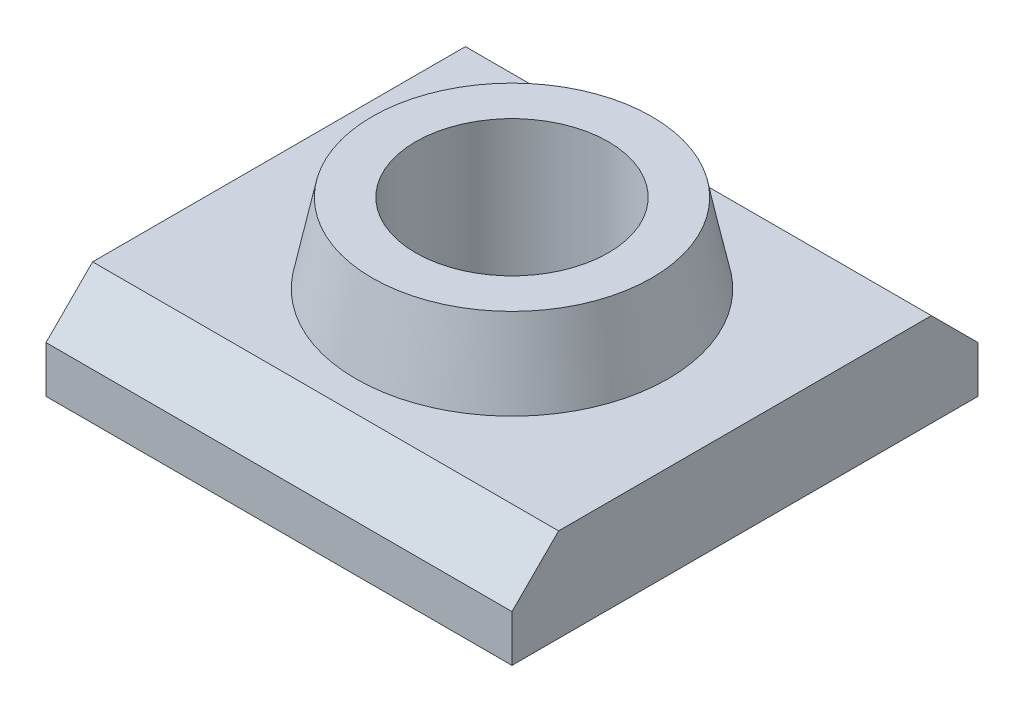
SolidWorks part; units mm, degrees
ref_plane "Front Plane" through (0, 0, 0) normal (0, 0, 1) x (1, 0, 0)
ref_plane "Top Plane" through (0, 0, 0) normal (0, 1, 0) x (1, 0, 0)
ref_plane "Right Plane" through (0, 0, 0) normal (1, 0, 0) x (0, 0, -1)
ref_plane "Plane1" through (-5, 0, 0) normal (1, 0, 0) x (0, 0, -1)
sketch "Sketch1" plane through (-5, 0, 0) normal (1, 0, 0) x (0, 0, -1)
  line L0 (4, -1.7) -> (-4, -1.7)
  line L1 (-4, -1.7) -> (-5, -2.7)
  line L2 (-5, -2.7) -> (-5, -3.7)
  line L3 (-5, -3.7) -> (5, -3.7)
  line L4 (5, -3.7) -> (5, -2.7)
  line L5 (5, -2.7) -> (4, -1.7)
  line L6 (0, 0) -> (0, -3.7) construction
  dimension "FIX_2" = 10
  dimension "E" = 2
  dimension "FIX_4" = 1
  dimension "FIX_3" = 1
  dimension "T" = 3.7
extrude "Boss-Extrude1" add sketch "Sketch1" along normal blind 10
sketch "Sketch2" plane through (0, 0, 0) normal (1, 0, 0) x (0, 0, -1)
  line L0 (0, 0) -> (0, -1.7) construction
  line L2 (3.35, -1.7) -> (3, 0)
  line L3 (3, 0) -> (0, 0)
  line L4 (0, 0) -> (0, -1.7)
  line L5 (0, -1.7) -> (3.35, -1.7)
  point P5 (-3.35, -1.7)
  point P9 (-3, 0)
  dimension "D" = 6.7
  dimension "FIX_7" = 6
  dimension "FIX_8" = 1.7
revolve "Revolve1" add sketch "Sketch2" angle 360 about L0
hole_wizard "Tapped Hole1" positions "Sketch4" profile "Sketch3" tap size "M5x0.8" standard "JIS" end condition through all
sketch "Sketch4" plane through (0, 0, 0) normal (0, 1, 0) x (1, 0, 0)
  point P0 (0, 0)
sketch "Sketch3" plane through (0, 0, 0) normal (1, 0, 0) x (0, 0, 1)
  line L0 (0, 0) -> (0, 3.7)
  line L1 (0, 3.7) -> (2.067, 3.7)
  line L2 (2.067, 3.7) -> (2.067, 0)
  line L5 (2.067, 0) -> (0, 0)
  line L11 (0, 0) -> (0, 3.7) construction
  dimension "Thru Tap Drill Dia." = 4.134
  dimension "Thru Tap Drill Depth" = 3.7
cosmetic thread "Thread1" parameters "NFIX_1"=5
